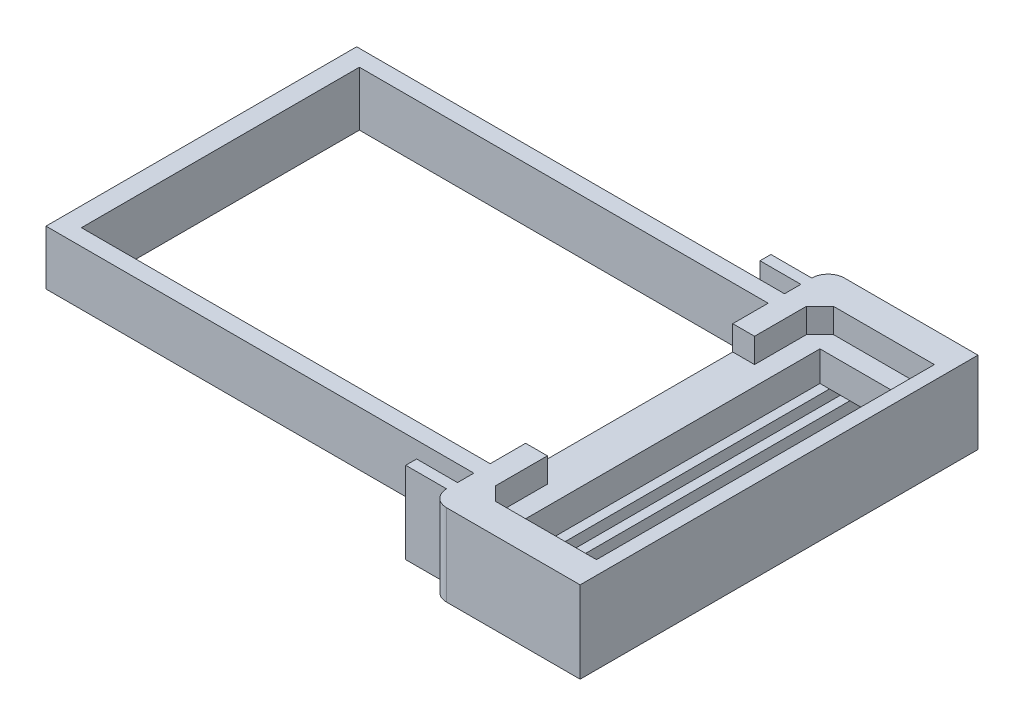
SolidWorks part; units mm, degrees
other "标注1"
sketch "草图5" plane through (20.5, 2.3, 12.3) normal (0.1352, 0.9908, 0.0046) x (0.1886, -0.0303, 0.9816)
other "标注2"
sketch "草图6" plane through (-0.7, 2.3, 12.3) normal (-0.5238, 0.8505, 0.0467) x (0.2914, 0.1274, 0.9481)
ref_plane "前视基准面" through (0, 0, 0) normal (0, 0, 1) x (1, 0, 0)
ref_plane "上视基准面" through (0, 0, 0) normal (0, 1, 0) x (1, 0, 0)
ref_plane "右视基准面" through (0, 0, 0) normal (1, 0, 0) x (0, 0, -1)
sketch "草图1" plane through (0, 0, 0) normal (0, 1, 0) x (1, 0, 0)
  line L0 (0, 0) -> (15, 0)
  line L1 (15, 0) -> (15, -10.2)
  line L2 (15, -10.2) -> (0, -10.2)
  line L3 (0, -10.2) -> (0, 0)
  line L4 (-0.7, 0.6) -> (-0.7, -10.8)
  line L5 (-0.7, -10.8) -> (15, -10.8)
  line L6 (15, -10.8) -> (15, -11.8)
  line L7 (15.6, -12.4) -> (20.5, -12.4)
  line L8 (20.5, -12.4) -> (20.5, 2.2)
  line L9 (20.5, 2.2) -> (15.6, 2.2)
  line L10 (15, 1.6) -> (15, 0.6)
  line L11 (15, 0.6) -> (-0.7, 0.6)
  line L12 (15, -5.1) -> (0, -5.1) construction
  line L13 (-0.7, -5.1) -> (20.5, -5.1) construction
  line L14 (20, -5.1) -> (16.5, -5.1) construction
  line L15 (16.5, 0.4) -> (20, 0.4)
  line L16 (16.5, 0.4) -> (16.5, -10.6)
  line L17 (16.5, -10.6) -> (20, -10.6)
  line L18 (20, 0.4) -> (20, -10.6)
  arc A0 (15.6, -12.4) -> (15, -11.8) centre (15.6, -11.8) cw
  arc A1 (15, 1.6) -> (15.6, 2.2) centre (15.6, 1.6) cw
  point P20 (15, -12.4)
  point P23 (15, 2.2)
  dimension "D7" = 0.6
  dimension "D1" = 15
  dimension "D2" = 10.2
  dimension "D3" = 11.4
  dimension "D4" = 0.7
  dimension "D5" = 5.5
  dimension "D6" = 1.6
  dimension "D8" = 0.5
  dimension "D9" = 3.5
  dimension "D10" = 11
extrude "凸台-拉伸1" add sketch "草图1" along normal blind 1.1
sketch "草图2" plane through (0, 1.1, 0) normal (0, 1, 0) x (1, 0, 0)
  line L1 (15, 0) -> (0, 0)
  line L2 (0, 0) -> (0, -10.2)
  line L3 (0, -10.2) -> (15, -10.2)
  line L5 (15, -10.8) -> (-0.7, -10.8)
  line L6 (-0.7, -10.8) -> (-0.7, 0.6)
  line L7 (-0.7, 0.6) -> (15, 0.6)
  line L8 (15, 0) -> (15, -1.3)
  line L9 (15, -10.2) -> (15, 0) construction
  line L10 (15, -1.3) -> (15.8, -1.3)
  line L11 (15.8, -1.3) -> (15.8, 0.6)
  line L12 (15.8, 0.6) -> (16.3, 1.1)
  line L13 (16.3, 1.1) -> (20, 1.1)
  line L14 (20, 1.1) -> (20, -11.3)
  line L15 (20, -11.3) -> (16.3, -11.3)
  line L16 (16.3, -11.3) -> (15.8, -10.8)
  line L17 (15.8, -10.8) -> (15.8, -8.9)
  line L18 (15.8, -8.9) -> (15, -8.9)
  line L19 (15, -8.9) -> (15, -10.2)
  line L20 (15, 0.6) -> (15, 1.6)
  line L21 (15.6, 2.2) -> (20.5, 2.2)
  line L22 (20.5, 2.2) -> (20.5, -12.4)
  line L23 (20.5, -12.4) -> (15.6, -12.4)
  line L24 (15, -11.8) -> (15, -10.8)
  arc A0 (15.6, -12.4) -> (15, -11.8) centre (15.6, -11.8) cw
  arc A1 (15, 1.6) -> (15.6, 2.2) centre (15.6, 1.6) cw
  dimension "D6" = 0.6
  dimension "D1" = 1.3
  dimension "D2" = 0.8
  dimension "D3" = 1.9
  dimension "D4" = 0.5
  dimension "D5" = 12.4
extrude "凸台-拉伸2" add sketch "草图2" along normal blind 0.9
sketch "草图3" plane through (0, 0, 0) normal (0, -1, 0) x (1, 0, 0)
  line L0 (15.6, 12.4) -> (20.5, 12.4) construction
  line L1 (20.5, -2.2) -> (15.6, -2.2)
  line L2 (20.5, -2.2) -> (20.5, 12.4)
  line L3 (20.5, 12.4) -> (15.6, 12.4)
  line L4 (15, -1.6) -> (15, 11.8)
  line L5 (15, 10.2) -> (15, 0) construction
  line L6 (19.5, 5.1) -> (20.5, 5.1) construction
  line L7 (16.85, -0.9) -> (17.25, -0.9)
  line L8 (16.85, -0.9) -> (16.85, 11.1)
  line L9 (16.85, 11.1) -> (17.25, 11.1)
  line L10 (17.25, -0.9) -> (17.25, 11.1)
  line L11 (17.6, -0.9) -> (18, -0.9)
  line L12 (17.6, -0.9) -> (17.6, 11.1)
  line L13 (17.6, 11.1) -> (18, 11.1)
  line L14 (18, -0.9) -> (18, 11.1)
  line L15 (18.35, -0.9) -> (18.75, -0.9)
  line L16 (18.35, -0.9) -> (18.35, 11.1)
  line L17 (18.35, 11.1) -> (18.75, 11.1)
  line L18 (18.75, -0.9) -> (18.75, 11.1)
  line L19 (19.1, -0.9) -> (19.5, -0.9)
  line L20 (19.1, -0.9) -> (19.1, 11.1)
  line L21 (19.1, 11.1) -> (19.5, 11.1)
  line L22 (19.5, -0.9) -> (19.5, 11.1)
  line L23 (17.25, -0.9) -> (17.6, -0.9) construction
  line L24 (18, -0.9) -> (18.35, -0.9) construction
  line L25 (18.75, -0.9) -> (19.1, -0.9) construction
  arc A0 (15.6, 12.4) -> (15, 11.8) centre (15.6, 11.8) ccw
  arc A1 (15.6, -2.2) -> (15, -1.6) centre (15.6, -1.6) cw
  dimension "D1" = 0.6
  dimension "D2" = 0.4
  dimension "D3" = 12
  dimension "D4" = 0.35
  dimension "D5" = 1
extrude "凸台-拉伸3" add sketch "草图3" along normal blind 1
sketch "草图4" plane through (15, 0, 0) normal (-1, 0, 0) x (0, 0, 1)
  line L0 (11.8, 2) -> (11.8, -1)
  line L1 (11.8, -1) -> (-1.6, -1)
  line L2 (-1.6, -1) -> (-1.6, 2)
  line L3 (-1.6, 2) -> (-1.2, 2)
  line L4 (-1.6, 2) -> (-0.6, 2) construction
  line L5 (-1.2, 2) -> (-1.2, -0.6)
  line L6 (-1.2, -0.6) -> (11.4, -0.6)
  line L7 (11.4, -0.6) -> (11.4, 2)
  line L8 (10.8, 2) -> (11.8, 2) construction
  line L9 (11.4, 2) -> (11.8, 2)
  line L10 (10.8, 2) -> (10.8, 0) construction
  line L11 (-0.6, 2) -> (-0.6, 0) construction
  line L12 (0, 0) -> (-0.6, 0) construction
  dimension "D1" = 0.6
  dimension "D2" = 0.6
  dimension "D3" = 0.6
extrude "凸台-拉伸4" add sketch "草图4" along normal blind 1.5
